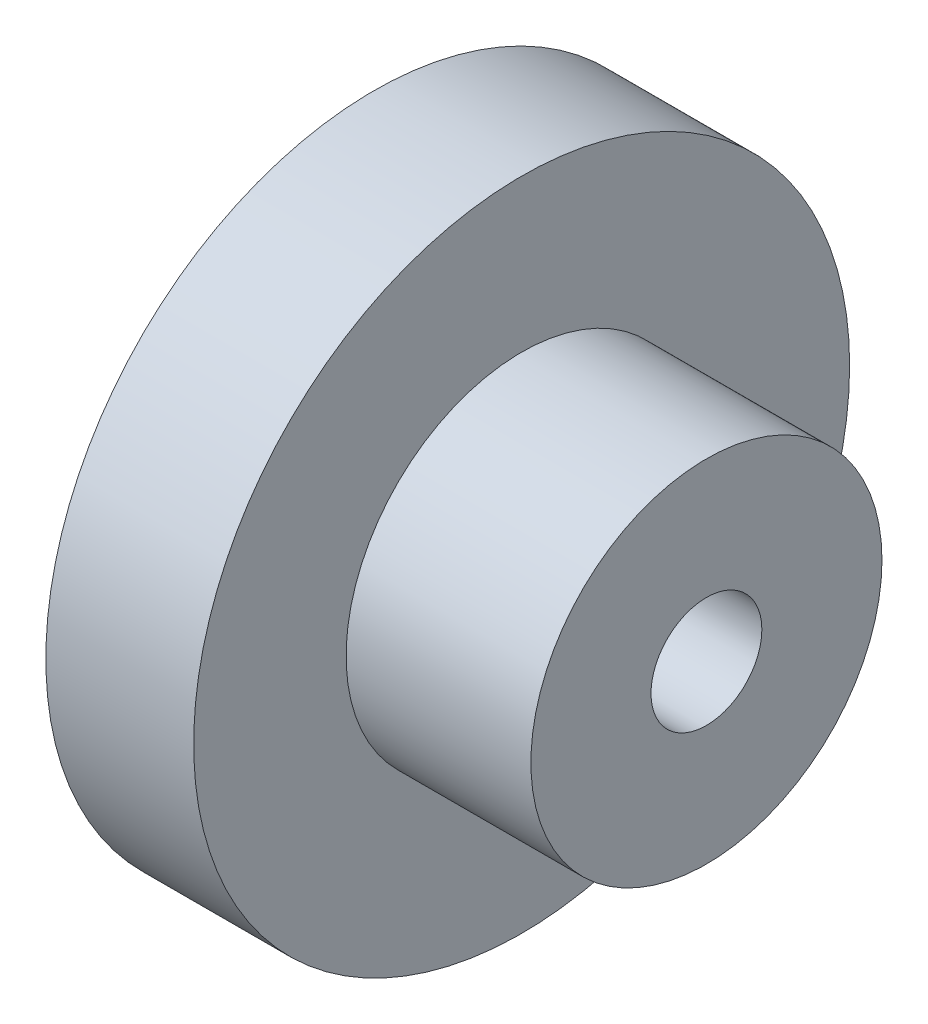
SolidWorks part; units mm, degrees
material "Delrin 2700 NC010, Low Viscosity Acetal Copolymer (SS)"
ref_plane "Front Plane" through (0, 0, 0) normal (0, 0, 1) x (1, 0, 0)
ref_plane "Top Plane" through (0, 0, 0) normal (0, 1, 0) x (1, 0, 0)
ref_plane "Right Plane" through (0, 0, 0) normal (1, 0, 0) x (0, 0, -1)
sketch "Sketch1" plane through (0, 0, 0) normal (1, 0, 0) x (0, 0, -1)
  circle A0 centre (0, 0) radius 8.875
  dimension "D1" = 17.75
extrude "Boss-Extrude1" add sketch "Sketch1" along normal blind 4
sketch "Sketch2" plane through (4, 0, 0) normal (1, 0, 0) x (0, 0, -1)
  circle A0 centre (0, 0) radius 4.75
  dimension "D1" = 9.5
extrude "Boss-Extrude2" add sketch "Sketch2" along normal blind 5
sketch "Sketch3" plane through (9, 0, 0) normal (1, 0, 0) x (0, 0, -1)
  circle A0 centre (0, 0) radius 1.5
  dimension "D1" = 3
extrude "Cut-Extrude1" cut sketch "Sketch3" against normal through all
equation "\"e\"=4.82414"
